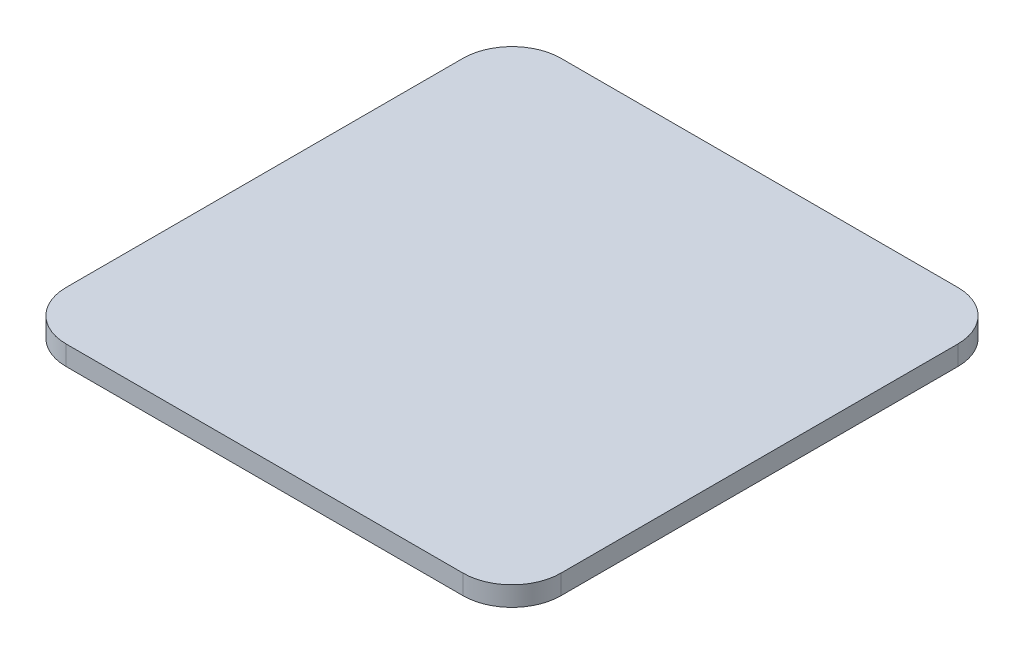
SolidWorks part; units mm, degrees
ref_plane "前视基准面" through (0, 0, 0) normal (0, 0, 1) x (1, 0, 0)
ref_plane "上视基准面" through (0, 0, 0) normal (0, 1, 0) x (1, 0, 0)
ref_plane "右视基准面" through (0, 0, 0) normal (1, 0, 0) x (0, 0, -1)
other "Configuration Table"
sketch "草图1" plane through (0, 0, 0) normal (0, 1, 0) x (1, 0, 0)
  line L1 (-20.25, 25.25) -> (20.25, 25.25)
  line L2 (-25.25, 20.25) -> (-25.25, -20.25)
  line L3 (-20.25, -25.25) -> (20.25, -25.25)
  line L4 (25.25, 20.25) -> (25.25, -20.25)
  line L5 (0, -25.25) -> (0, 25.25) construction
  line L6 (-25.25, 0) -> (25.25, 0) construction
  arc A0 (-20.25, -25.25) -> (-25.25, -20.25) centre (-20.25, -20.25) cw
  arc A1 (20.25, -25.25) -> (25.25, -20.25) centre (20.25, -20.25) ccw
  arc A2 (25.25, 20.25) -> (20.25, 25.25) centre (20.25, 20.25) ccw
  arc A3 (-20.25, 25.25) -> (-25.25, 20.25) centre (-20.25, 20.25) ccw
  point P0 (0, 0)
  point P8 (25.25, -25.25)
  point P11 (25.25, 25.25)
  point P15 (-25.25, 25.25)
  dimension "D3" = 5
  dimension "D1" = 50.5
  dimension "D2" = 50.5
extrude "凸台-拉伸1" add sketch "草图1" along normal blind 2
